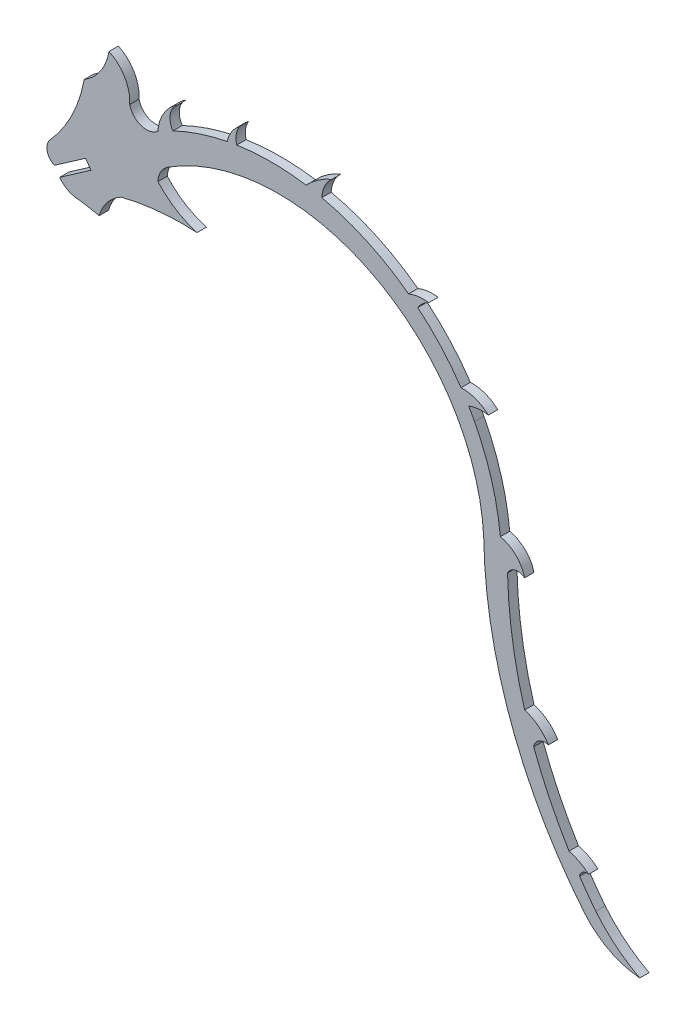
SolidWorks part; units mm, degrees
ref_plane "Front Plane" through (0, 0, 0) normal (0, 0, 1) x (1, 0, 0)
ref_plane "Top Plane" through (0, 0, 0) normal (0, 1, 0) x (1, 0, 0)
ref_plane "Right Plane" through (0, 0, 0) normal (1, 0, 0) x (0, 0, -1)
sketch "Sketch1" plane through (0, 0, 0) normal (0, 0, 1) x (1, 0, 0)
  line L3 (-39.1177, 31.7057) -> (-34.0351, 35.2455)
  line L4 (-34.0351, 35.2455) -> (-34.9073, 36.4982)
  line L5 (-34.9073, 36.4982) -> (-39.99, 32.9575)
  arc A0 (29.8946, 15.3099) -> (46.2769, -29.2493) centre (101.8998, 16.4917) ccw
  arc A1 (32.5961, 16.9178) -> (36.5456, 13.0856) centre (31.4773, 11.8135) cw
  arc A2 (36.5456, 13.0856) -> (33.7666, 12.3881) centre (35.4344, 11.6278) ccw
  arc A3 (33.7666, 12.3881) -> (36.5456, -5.5371) centre (101.9943, 13.7877) ccw
  arc A4 (46.2769, -29.2493) -> (55.2839, -33.9416) centre (56.294, -21.0117) ccw
  arc A5 (55.2839, -33.9416) -> (48.124, -28.1046) centre (66.0056, -13.4799) cw
  arc A6 (36.5456, -5.5371) -> (40.4113, -8.5298) centre (34.6077, -12.0334) cw
  arc A7 (40.4113, -8.5298) -> (38.022, -9.9722) centre (39.8428, -10.2881) ccw
  arc A8 (43.7733, -21.8114) -> (46.9611, -23.4879) centre (41.8293, -29.377) cw
  arc A9 (-40.7294, 36.1534) -> (-39.99, 32.9575) centre (-39.1554, 34.8341) ccw
  arc A10 (-40.7294, 36.1534) -> (-35.1496, 47.4069) centre (-57.7843, 51.6197) ccw
  arc A11 (-35.1501, 47.4663) -> (-35.1496, 47.4069) centre (-31.4335, 47.4663) ccw
  arc A12 (-27.7227, 47.6771) -> (-23.1538, 46.181) centre (-24.9951, 48.2822) ccw
  arc A13 (28.393, 31.0321) -> (27.4367, 32.7559) centre (-4.6654, 13.818) ccw
  arc A14 (26.1992, 34.712) -> (19.1513, 42.4876) centre (-4.6654, 13.818) ccw
  arc A15 (17.6539, 43.6682) -> (3.5426, 50.1747) centre (-4.6654, 13.818) ccw
  arc A16 (0.9863, 50.6588) -> (-10.3055, 50.6605) centre (-4.6654, 13.818) ccw
  arc A17 (-11.8506, 50.3906) -> (-20.7027, 47.463) centre (-4.6654, 13.818) ccw
  arc A18 (32.5961, 16.9178) -> (28.393, 31.0321) centre (-6.0728, 13.0856) ccw
  arc A19 (46.9611, -23.4879) -> (45.4931, -24.4823) centre (46.6876, -24.6649) ccw
  arc A20 (45.4931, -24.4823) -> (48.124, -28.1046) centre (101.9943, 13.7877) ccw
  arc A21 (38.022, -9.9722) -> (43.7733, -21.8114) centre (101.9943, 13.7877) ccw
  arc A23 (29.8946, 15.3099) -> (-21.4776, 41.9665) centre (-3.4996, 13.7834) ccw
  arc A24 (-21.4776, 41.9665) -> (-23.1366, 39.1004) centre (-19.5423, 38.9331) ccw
  arc A25 (-39.1177, 31.7057) -> (-36.0303, 30.1162) centre (-36.0303, 33.9093) ccw
  arc A26 (-19.9548, 51.4772) -> (-23.1538, 46.181) centre (-16.2496, 45.6251) ccw
  arc A27 (-19.9548, 51.4772) -> (-20.7027, 47.463) centre (-18.2158, 49.0764) ccw
  arc A28 (-9.8923, 53.4498) -> (-11.8506, 50.3906) centre (-6.8711, 49.3595) ccw
  arc A29 (-9.8923, 53.4498) -> (-10.3055, 50.6605) centre (-6.9152, 51.5836) ccw
  arc A30 (5.181, 53.5774) -> (0.9863, 50.6588) centre (10.009, 42.165) ccw
  arc A31 (5.181, 53.5774) -> (3.5426, 50.1747) centre (8.3461, 49.9576) ccw
  arc A32 (20.9427, 44.0699) -> (17.6539, 43.6682) centre (20.0459, 37.7484) ccw
  arc A33 (20.9427, 44.0699) -> (19.1513, 42.4876) centre (22.7574, 40.2103) ccw
  arc A34 (30.6516, 33.0797) -> (26.1992, 34.712) centre (26.4465, 28.498) ccw
  arc A35 (30.6516, 33.0797) -> (27.4367, 32.7559) centre (29.6562, 26.841) ccw
  arc A36 (-16.7671, 35.0937) -> (-29.1141, 33.9162) centre (-19.0517, -6.2719) ccw
  arc A37 (-23.1366, 39.1004) -> (-16.7671, 35.0937) centre (-13.1571, 47.8988) ccw
  arc A40 (-29.1141, 33.9162) -> (-32.7065, 29.4979) centre (-25.6462, 27.427) ccw
  arc A41 (-32.7065, 29.4979) -> (-36.0303, 30.1162) centre (-41.9324, -10.8584) ccw
  arc A42 (-35.1501, 47.4663) -> (-31.0924, 53.467) centre (-39.7541, 54.9519) ccw
  arc A43 (-27.7227, 47.6771) -> (-31.0924, 53.467) centre (-33.7374, 48.052) ccw
extrude "Boss-Extrude1" add sketch "Sketch1" along normal blind 1.524
